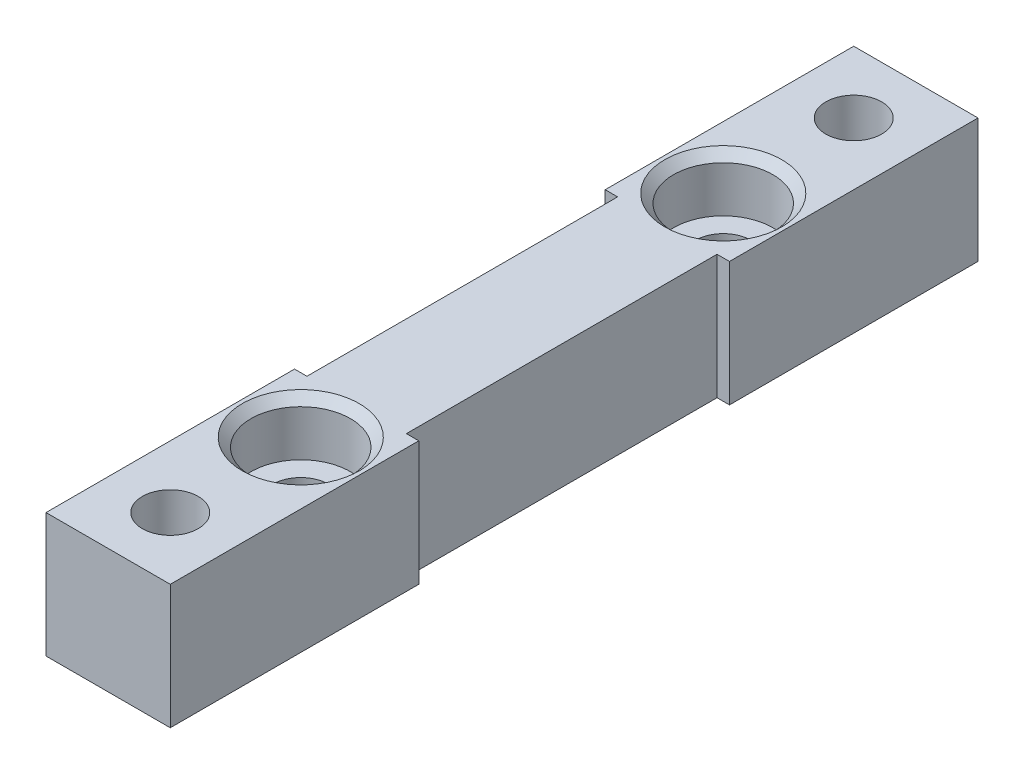
SolidWorks part; units mm, degrees
ref_plane "정면" through (0, 0, 0) normal (0, 0, 1) x (1, 0, 0)
ref_plane "윗면" through (0, 0, 0) normal (0, 1, 0) x (1, 0, 0)
ref_plane "우측면" through (0, 0, 0) normal (1, 0, 0) x (0, 0, -1)
sketch "스케치1" plane through (0, 0, 0) normal (0, 1, 0) x (1, 0, 0)
  line L0 (0, -17) -> (0, 17)
  line L14 (-5, 32.5) -> (5, 32.5)
  line L15 (-5, 32.5) -> (-5, 12.5)
  line L16 (-5, 12.5) -> (5, 12.5)
  line L17 (5, 32.5) -> (5, 12.5)
  line L18 (-5, 32.5) -> (5, 12.5) construction
  line L19 (-5, 12.5) -> (5, 32.5) construction
  line L20 (-4, 12.5) -> (4, 12.5)
  line L21 (-4, 12.5) -> (-4, -12.5)
  line L22 (-4, 0) -> (4, 0)
  line L23 (4, 12.5) -> (4, -12.5)
  line L24 (-4, 12.5) -> (4, 0) construction
  line L25 (-4, 0) -> (4, 12.5) construction
  line L26 (-4, 0) -> (4, -12.5) construction
  line L27 (-4, -12.5) -> (4, 0) construction
  line L28 (-5, -12.5) -> (5, -32.5) construction
  line L29 (-5, -32.5) -> (5, -12.5) construction
  line L30 (-4, -12.5) -> (4, -12.5)
  line L31 (5, -32.5) -> (5, -12.5)
  line L32 (-5, -12.5) -> (5, -12.5)
  line L33 (-5, -32.5) -> (-5, -12.5)
  line L34 (-5, -32.5) -> (5, -32.5)
  point P0 (0, 22.5)
  point P5 (0, 6.25)
  point P18 (0, -6.25)
  point P20 (0, 0)
  point P21 (0, -22.5)
  dimension "D1" = 10
  dimension "D2" = 20
  dimension "D3" = 32.5
  dimension "D4" = 8
  dimension "D5" = 17
extrude "보스-돌출1" add sketch "스케치1" along normal blind 10
hole_wizard "M4 육각 소켓 머리 캡 나사용 카운터보어1" positions "스케치2" profile "스케치3" counterbore size "M4" standard "ISO" end condition up to next
sketch "스케치2" plane through (0, 10, 0) normal (0, 1, 0) x (1, 0, 0)
  line L0 (0, 17) -> (0, -17)
  line L2 (4, 12.5) -> (4, -12.5) construction
  line L3 (4, 12.5) -> (4, -12.5)
  point P1 (0, 17)
  point P2 (0, -17)
  point P13 (4, 0)
  point P14 (0, 0)
  dimension "D1" = 34
sketch "스케치3" plane through (0, 10, -17) normal (1, 0, 0) x (0, 0, 1)
  line L0 (0, 0) -> (0, 10)
  line L1 (0, 10) -> (2.25, 10)
  line L3 (2.25, 10) -> (2.25, 4.4)
  line L4 (4, 4.4) -> (2.25, 4.4)
  line L5 (4, 4.4) -> (4, 0.7)
  line L6 (4, 0.7) -> (4.7, 0)
  line L7 (4.7, 0) -> (0, 0)
  line L8 (-4, 0.7) -> (-4.7, 0) construction
  line L11 (0, -6.35) -> (0, 107.95) construction
  dimension "관통 구멍 지름" = 4.5
  dimension "관통 구멍 깊이" = 10
  dimension "카운터보어 지름" = 8
  dimension "카운터보어 깊이" = 4.4
  dimension "표면 카운터싱크 지름" = 9.4
  dimension "표면 카운터싱크 각도" = 90
hole_wizard "M4 여유 구멍1" positions "스케치4" profile "스케치6" hole size "M4" standard "ISO" end condition up to next
sketch "스케치4" plane through (0, 0, 0) normal (0, -1, 0) x (-1, 0, 0)
  line L0 (0, -27.5) -> (0, 27.5)
  line L2 (-4, 12.5) -> (-4, -12.5) construction
  line L3 (-4, 12.5) -> (-4, -12.5)
  point P1 (0, -27.5)
  point P2 (0, 27.5)
  point P7 (0, 0)
  point P8 (-4, 0)
  point P13 (54.1084, -109.4208)
  dimension "D1" = 55
sketch "스케치6" plane through (0, 0, 27.5) normal (1, 0, 0) x (0, 0, -1)
  line L0 (0, 0) -> (0, 10)
  line L1 (0, 10) -> (2.25, 10)
  line L2 (2.25, 10) -> (2.25, 0)
  line L5 (2.25, 0) -> (0, 0)
  line L11 (0, -6.35) -> (0, 107.95) construction
  dimension "관통 구멍 지름" = 4.5
  dimension "관통 구멍 깊이" = 10
sketch "스케치7" plane through (0, 0, 0) normal (0, -1, 0) x (1, 0, 0)
  line L0 (-5, -32.5) -> (5, -32.5) construction
  line L1 (2.0496, -23.95) -> (-2.0496, -23.95)
  line L2 (-2.0496, -23.95) -> (-4.0992, -27.5)
  line L3 (-4.0992, -27.5) -> (-2.0496, -31.05)
  line L4 (-2.0496, -31.05) -> (2.0496, -31.05)
  line L5 (2.0496, -31.05) -> (4.0992, -27.5)
  line L6 (4.0992, -27.5) -> (2.0496, -23.95)
  line L7 (-4, 0) -> (4, 0)
  line L8 (-4, -12.5) -> (-4, 12.5) construction
  line L9 (4, -12.5) -> (4, 12.5) construction
  line L10 (4.0992, 27.5) -> (2.0496, 23.95)
  line L11 (2.0496, 31.05) -> (4.0992, 27.5)
  line L12 (-2.0496, 31.05) -> (2.0496, 31.05)
  line L13 (-4.0992, 27.5) -> (-2.0496, 31.05)
  line L14 (-2.0496, 23.95) -> (-4.0992, 27.5)
  line L15 (2.0496, 23.95) -> (-2.0496, 23.95)
  circle A0 centre (0, -27.5) radius 3.55 construction
  circle A1 centre (0, 27.5) radius 3.55 construction
  circle M4 centre (0, -27.5) radius 2.25
  circle M19 centre (0, 27.5) radius 2.25
  dimension "D1" = 7.1
extrude "컷-돌출1" cut sketch "스케치7" against normal blind 4 contours L5 L6 L1 L2 L3 L4 M4 | L15 L10 L11 L12 L13 L14 M19
